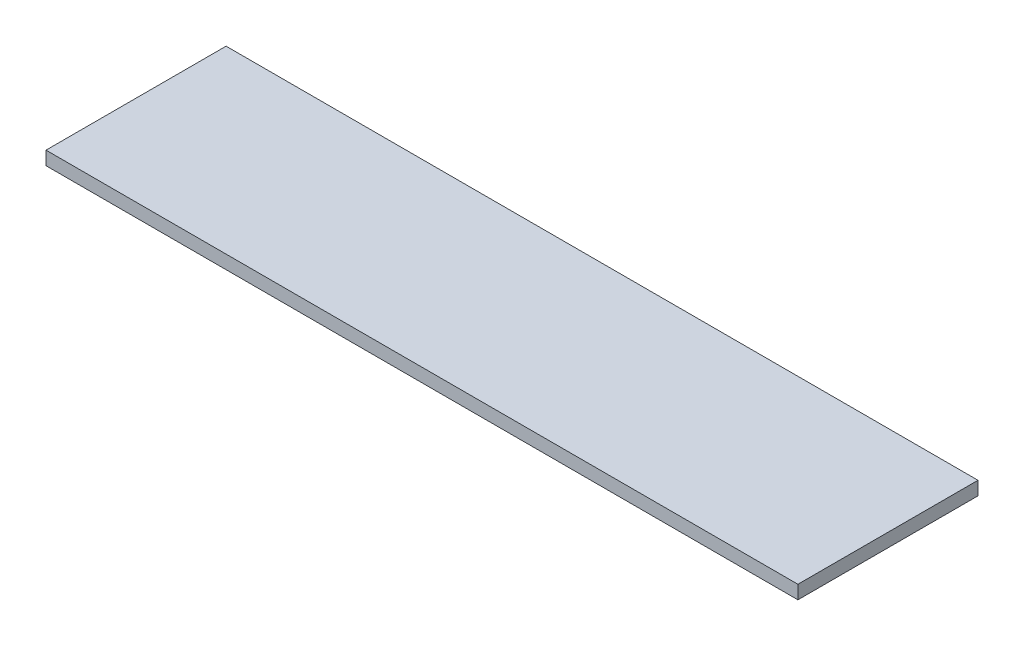
SolidWorks part; units mm, degrees
ref_plane "Front Plane" through (0, 0, 0) normal (0, 0, 1) x (1, 0, 0)
ref_plane "Top Plane" through (0, 0, 0) normal (0, 1, 0) x (1, 0, 0)
ref_plane "Right Plane" through (0, 0, 0) normal (1, 0, 0) x (0, 0, -1)
sketch "Sketch1" plane through (0, 0, 0) normal (0, 1, 0) x (1, 0, 0)
  line L1 (-530.225, -127) -> (530.225, -127)
  line L2 (-530.225, -127) -> (-530.225, 127)
  line L3 (-530.225, 127) -> (530.225, 127)
  line L4 (530.225, -127) -> (530.225, 127)
  line L5 (-530.225, -127) -> (530.225, 127) construction
  line L6 (-530.225, 127) -> (530.225, -127) construction
  point P0 (0, 0)
  dimension "D1" = 254
  dimension "D2" = 1060.45
extrude "Boss-Extrude1" add sketch "Sketch1" along normal blind 19.05
